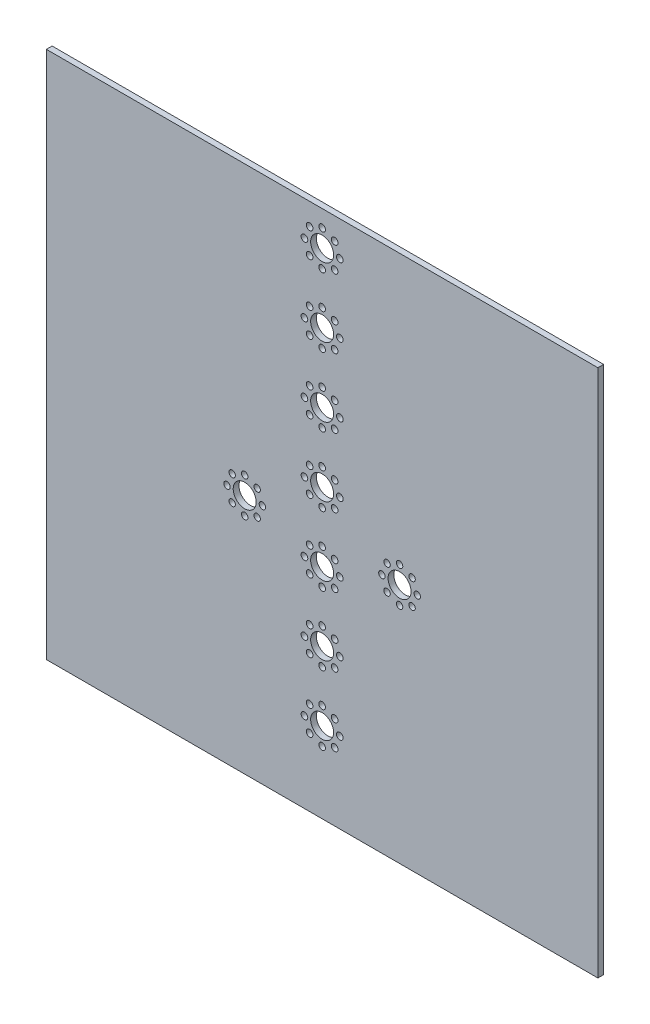
SolidWorks part; units mm, degrees
material "6061-T6 (SS)"
ref_plane "Front Plane" through (0, 0, 0) normal (0, 0, 1) x (1, 0, 0)
ref_plane "Top Plane" through (0, 0, 0) normal (0, 1, 0) x (1, 0, 0)
ref_plane "Right Plane" through (0, 0, 0) normal (1, 0, 0) x (0, 0, -1)
sketch "Sketch1" plane through (0, 0, 0) normal (0, 0, 1) x (1, 0, 0)
  line L1 (0, 0) -> (-304.8, 0)
  line L2 (0, 0) -> (0, -292.1)
  line L3 (0, -292.1) -> (-304.8, -292.1)
  line L4 (-304.8, 0) -> (-304.8, -292.1)
  dimension "D1" = 292.1
  dimension "D2" = 304.8
extrude "Boss-Extrude1" add sketch "Sketch1" along normal blind 3.175
sketch "Sketch2" plane through (0, 0, 0) normal (0, 0, -1) x (-1, 0, 0)
  line L0 (0, -158.75) -> (304.8, -158.75) construction
  line L1 (0, -292.1) -> (0, 0) construction
  line L2 (304.8, 0) -> (304.8, -292.1) construction
  line L3 (304.8, -292.1) -> (0, -292.1) construction
  circle A0 centre (99.822, -158.75) radius 1.778
  point P12 (109.601, -158.75)
  dimension "D2" = 109.601
  dimension "D3" = 3.556
  dimension "D1" = 133.35
  dimension "D5" = 9.779
extrude "Cut-Extrude1" cut sketch "Sketch2" against normal blind 3.175
ref_plane "Plane1" through (-152.4, 0, 0) normal (1, 0, 0) x (0, 0, -1)
mirror "Mirror1" about plane through (-152.4, 0, 0) normal (1, 0, 0) of "Cut-Extrude1"
sketch "Sketch3" plane through (0, 0, 0) normal (0, 0, -1) x (-1, 0, 0)
  line L2 (304.8, -292.1) -> (0, -292.1) construction
  line L3 (0, -292.1) -> (0, 0) construction
  circle A0 centre (109.601, -158.75) radius 6.35
  dimension "D3" = 12.7
  dimension "D1" = 133.35
  dimension "D2" = 109.601
extrude "Cut-Extrude2" cut sketch "Sketch3" against normal blind 3.175 contours A0
pattern_circular "CirPattern1" count 8 over 360 about axis through (-109.601, -158.75, 0) along (0, 0, 1) of "Cut-Extrude1"
mirror "Mirror2" about plane through (-152.4, 0, 0) normal (1, 0, 0) of "CirPattern1", "Cut-Extrude2"
sketch "Sketch4" plane through (0, 0, 0) normal (0, 0, -1) x (-1, 0, 0)
  line L0 (152.4, 1.7462) -> (152.4, -1.7463) construction
  line L1 (0, 0) -> (304.8, 0) construction
  circle A0 centre (152.4, -19.05) radius 6.35
  dimension "D1" = 12.7
  dimension "D2" = 19.05
extrude "Cut-Extrude3" cut sketch "Sketch4" against normal blind 3.175
sketch "Sketch5" plane through (0, 0, 0) normal (0, 0, -1) x (-1, 0, 0)
  line L0 (152.4, 1.7462) -> (152.4, -1.7463) construction
  circle A0 centre (152.4, -9.271) radius 1.8415
  circle A1 centre (152.4, -19.05) radius 6.35 construction
  dimension "D1" = 3.683
  dimension "D2" = 9.779
extrude "Cut-Extrude4" cut sketch "Sketch5" against normal blind 3.175
pattern_circular "CirPattern2" count 8 over 360 about axis through (-152.4, -19.05, 0) along (0, 0, 1) of "Cut-Extrude4"
pattern_linear "LPattern1" count 7 spacing 38.1 along (0, -1, 0) of "CirPattern2", "Cut-Extrude3", "Cut-Extrude4"
